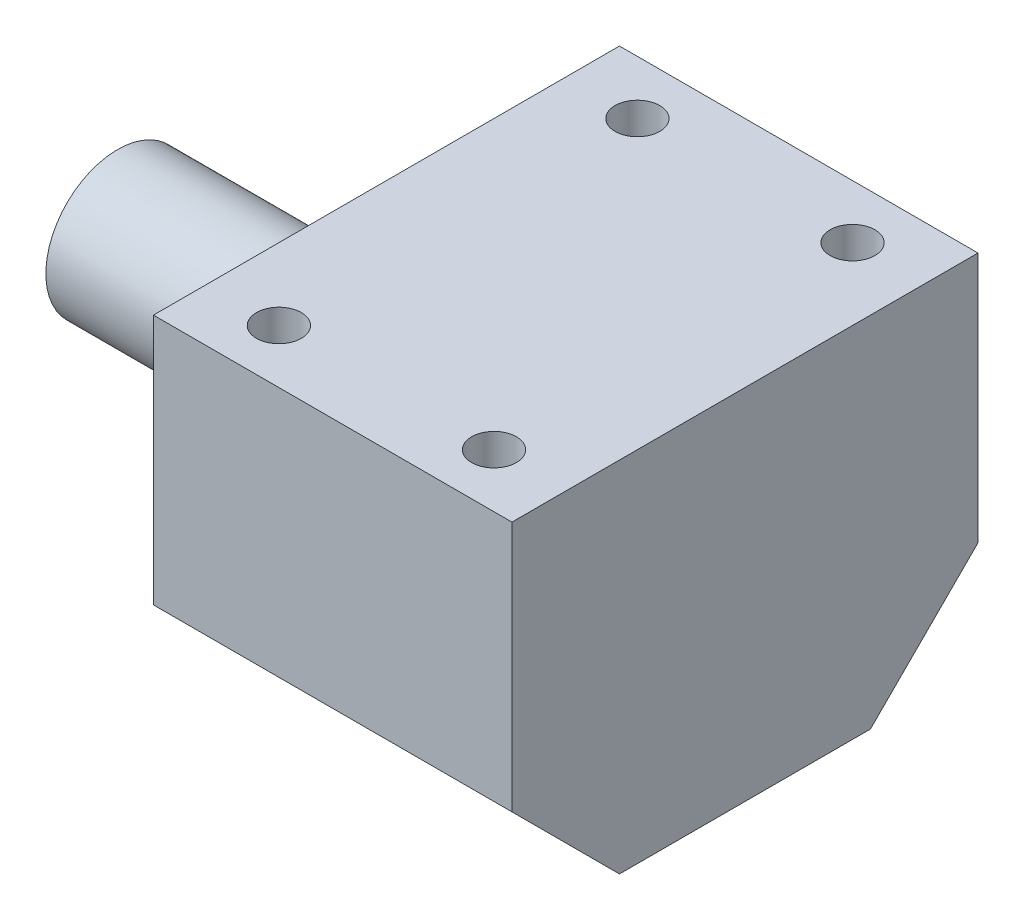
SolidWorks part; units mm, degrees
ref_plane "Front Plane" through (0, 0, 0) normal (0, 0, 1) x (1, 0, 0)
ref_plane "Top Plane" through (0, 0, 0) normal (0, 1, 0) x (1, 0, 0)
ref_plane "Right Plane" through (0, 0, 0) normal (1, 0, 0) x (0, 0, -1)
sketch "Sketch1" plane through (0, 0, 0) normal (1, 0, 0) x (0, 0, -1)
  circle A0 centre (0, 0) radius 8
  dimension "D1" = 16
extrude "Boss-Extrude1" add sketch "Sketch1" along normal blind 150
sketch "Sketch2" plane through (0, 0, 0) normal (0, 1, 0) x (1, 0, 0)
  line L0 (150, -8) -> (150, 8) construction
  line L1 (70, -26) -> (30, -26)
  line L2 (70, -26) -> (70, 26)
  line L3 (70, 26) -> (30, 26)
  line L4 (30, -26) -> (30, 26)
  line L5 (70, -26) -> (30, 26) construction
  line L6 (70, 26) -> (30, -26) construction
  point P0 (50, 0)
  dimension "D1" = 40
  dimension "D2" = 52
  dimension "D3" = 100
extrude "Boss-Extrude2" add sketch "Sketch2" along normal mid plane 40
chamfer "Chamfer1" distance 12 angle 45 2 edges at (50, -20, 26) (50, -20, -26)
sketch "Sketch3" plane through (0, 20, 0) normal (0, 1, 0) x (1, 0, 0)
  line L0 (30, 26) -> (70, 26) construction
  line L1 (62, -20) -> (38, -20) construction
  line L2 (62, -20) -> (62, 20) construction
  line L3 (62, 20) -> (38, 20) construction
  line L4 (38, -20) -> (38, 20) construction
  line L5 (62, -20) -> (38, 20) construction
  line L6 (62, 20) -> (38, -20) construction
  line L7 (70, -26) -> (70, 26) construction
  line L8 (70, 26) -> (30, 26) construction
  line L9 (70, 26) -> (70, -26) construction
  circle A0 centre (38, 20) radius 2.5
  circle A1 centre (62, 20) radius 2.5
  circle A2 centre (38, -20) radius 2.5
  circle A3 centre (62, -20) radius 2.5
  point P0 (50, 0)
  point P12 (50, 26)
  point P15 (70, 0)
  dimension "D3" = 5
  dimension "D1" = 40
  dimension "D2" = 24
extrude "Cut-Extrude1" cut sketch "Sketch3" against normal blind 10
sketch "Sketch4" plane through (0, 20, 0) normal (0, 1, 0) x (1, 0, 0)
  line L0 (70, -26) -> (70, 26) construction
  line L1 (150.3514, -71.8772) -> (70, -71.8772)
  line L2 (150.3514, -71.8772) -> (150.3514, 34.1027)
  line L3 (150.3514, 34.1027) -> (70, 34.1027)
  line L4 (70, -71.8772) -> (70, 34.1027)
  line L5 (150.3514, -71.8772) -> (70, 34.1027) construction
  line L6 (150.3514, 34.1027) -> (70, -71.8772) construction
  point P0 (110.1757, -18.8872)
extrude "Cut-Extrude2" cut sketch "Sketch4" against normal through all
